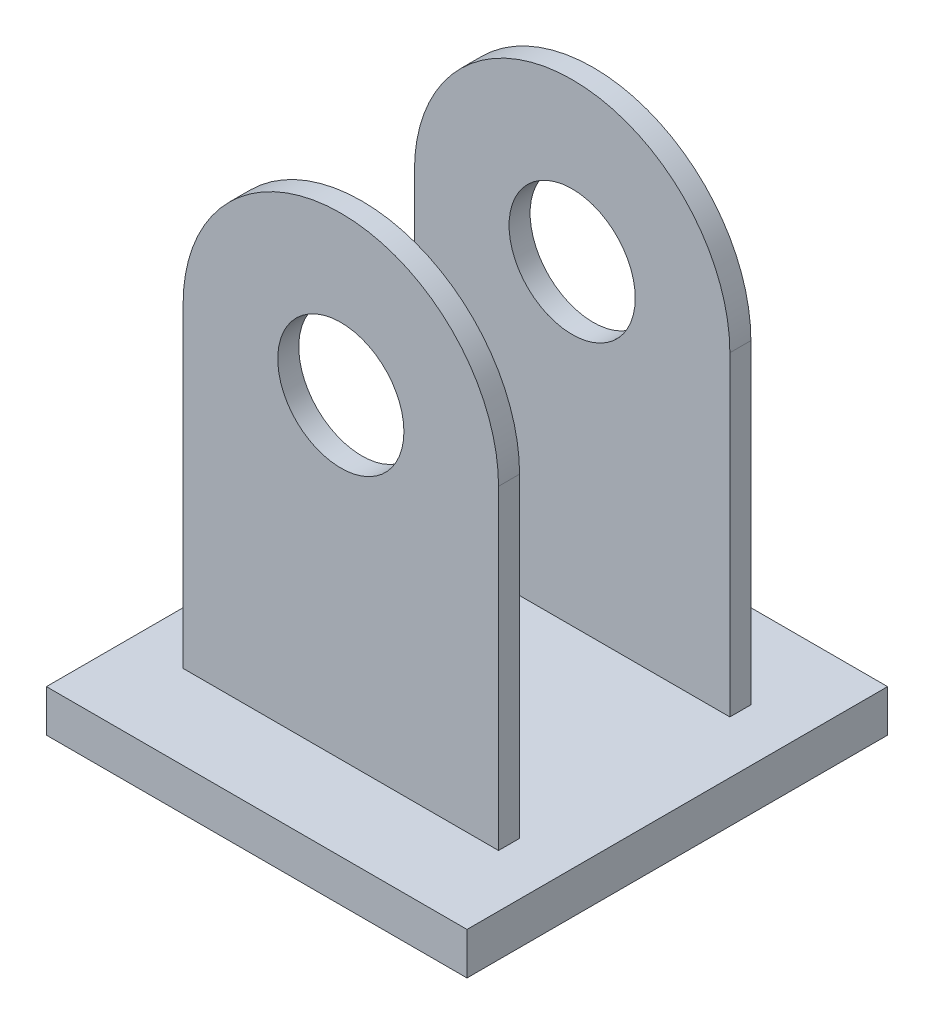
SolidWorks part; units mm, degrees
ref_plane "Plano frontal" through (0, 0, 0) normal (0, 0, 1) x (1, 0, 0)
ref_plane "Plano superior" through (0, 0, 0) normal (0, 1, 0) x (1, 0, 0)
ref_plane "Plano direito" through (0, 0, 0) normal (1, 0, 0) x (0, 0, -1)
sketch "Sketch1" plane through (0, 0, 0) normal (0, 1, 0) x (1, 0, 0)
  line L1 (-10, -10) -> (10, -10)
  line L2 (-10, -10) -> (-10, 10)
  line L3 (-10, 10) -> (10, 10)
  line L4 (10, -10) -> (10, 10)
  line L5 (-10, -10) -> (10, 10) construction
  line L6 (-10, 10) -> (10, -10) construction
  point P0 (0, 0)
  dimension "D1" = 20
extrude "Boss-Extrude1" add sketch "Sketch1" along normal blind 2
ref_plane "Plane1" through (0, 0, 5) normal (0, 0, 1) x (1, 0, 0)
sketch "Sketch4" plane through (0, 0, 5) normal (0, 0, 1) x (1, 0, 0)
  line L0 (0, -3.9641) -> (0, 24.5) construction
  line L1 (0, -11) -> (0, 11) construction
  line L2 (-10, 2) -> (10, 2) construction
  line L4 (-7.5, 17) -> (-7.5, 2)
  line L5 (-7.5, 2) -> (7.5, 2)
  line L6 (7.5, 17) -> (7.5, 2)
  line L7 (-7.5, 17) -> (7.5, 2) construction
  line L8 (-7.5, 2) -> (7.5, 17) construction
  arc A0 (-7.5, 17) -> (7.5, 17) centre (0, 17) cw
  circle A1 centre (0, 17) radius 3
  point P5 (0, 9.5)
  point P14 (0, 24.5)
  dimension "D3" = 6
  dimension "D1" = 15
  dimension "D2" = 7.5
  dimension "D4" = 15
extrude "Boss-Extrude2" add sketch "Sketch4" along normal blind 1
mirror "Mirror1" about plane through (0, 0, 0) normal (0, 0, 1) of "Boss-Extrude2"
